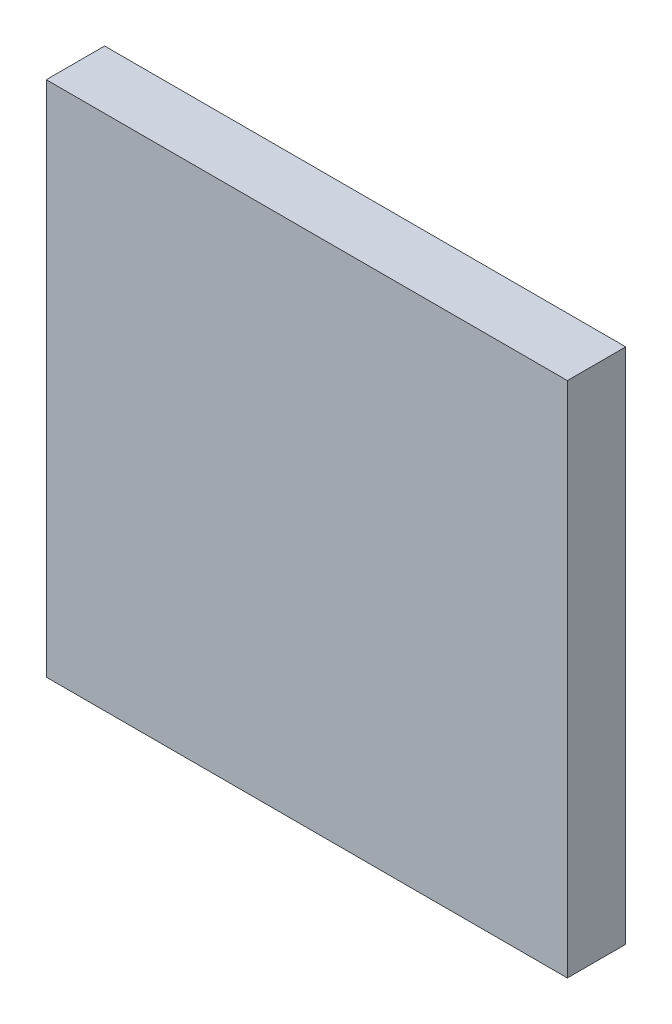
SolidWorks part; units mm, degrees
ref_plane "Front Plane" through (0, 0, 0) normal (0, 0, 1) x (1, 0, 0)
ref_plane "Top Plane" through (0, 0, 0) normal (0, 1, 0) x (1, 0, 0)
ref_plane "Right Plane" through (0, 0, 0) normal (1, 0, 0) x (0, 0, -1)
sketch "Sketch1" plane through (0, 0, 0) normal (0, 0, 1) x (1, 0, 0)
  line L0 (-4.4635, 4.4635) -> (4.4635, 4.4635)
  line L1 (4.4635, 4.4635) -> (4.4635, -4.4)
  line L2 (4.4635, -4.4) -> (-4.4635, -4.4)
  line L3 (-4.4635, -4.4) -> (-4.4635, 4.4635)
extrude "Component_Outline" add sketch "Sketch1" along normal blind 1 separate body
sketch3d "3DSketch1"
  line L0 (0, 0, 0) -> (1, 0, 0)
  line L1 (0, 0, 0) -> (0, 1, 0)
  line L2 (0, 0, 0) -> (0, 0, 1)
  point P0 (0, 0, 0)
